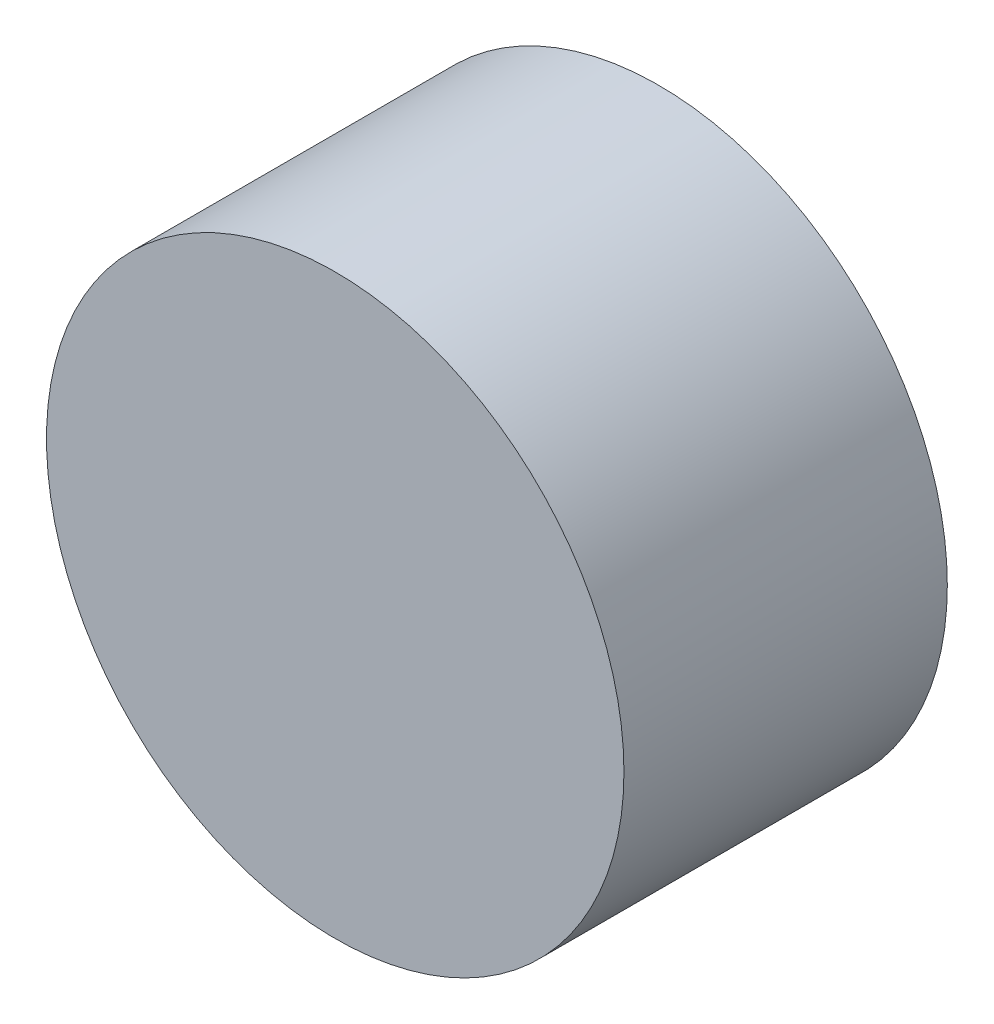
SolidWorks part; units mm, degrees
ref_plane "Front Plane" through (0, 0, 0) normal (0, 0, 1) x (1, 0, 0)
ref_plane "Top Plane" through (0, 0, 0) normal (0, 1, 0) x (1, 0, 0)
ref_plane "Right Plane" through (0, 0, 0) normal (1, 0, 0) x (0, 0, -1)
sketch "Sketch1" plane through (0, 0, 0) normal (0, 0, 1) x (1, 0, 0)
  circle A0 centre (0, 0) radius 25
extrude "Boss-Extrude1" add sketch "Sketch1" along normal blind 28
